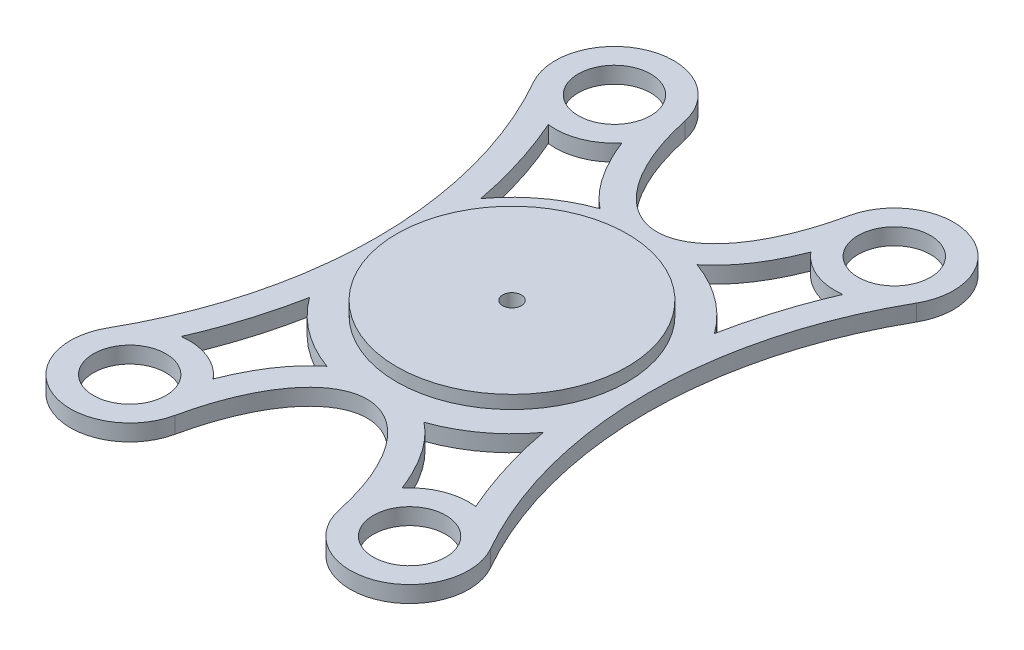
SolidWorks part; units mm, degrees
material "ABS"
ref_plane "Front Plane" through (0, 0, 0) normal (0, 0, 1) x (1, 0, 0)
ref_plane "Top Plane" through (0, 0, 0) normal (0, 1, 0) x (1, 0, 0)
ref_plane "Right Plane" through (0, 0, 0) normal (1, 0, 0) x (0, 0, -1)
sketch "Sketch1" plane through (0, 0, 0) normal (0, 1, 0) x (1, 0, 0)
  line L1 (-50, -50) -> (50, -50)
  line L2 (-50, -50) -> (-50, 50)
  line L3 (-50, 50) -> (50, 50)
  line L4 (50, -50) -> (50, 50)
  line L5 (-50, -50) -> (50, 50) construction
  line L6 (-50, 50) -> (50, -50) construction
  point P0 (0, 0)
  dimension "D1" = 100
  dimension "D2" = 100
extrude "Boss-Extrude1" add sketch "Sketch1" along normal blind 2.5
sketch "Sketch2" plane through (0, 2.5, 0) normal (0, 1, 0) x (1, 0, 0)
  line L0 (50, 50) -> (-50, 50) construction
  line L1 (-50, -50) -> (50, -50) construction
  line L2 (-21.25, 36.8061) -> (21.25, -36.8061)
  line L3 (21.25, 36.8061) -> (-21.25, -36.8061)
  line L14 (0, -15.9125) -> (0, 15.9125)
  arc A0 (-29.0749, 32.3597) -> (-12.4502, 38.6938) centre (-21.25, 36.8061) cw
  circle A1 centre (21.25, 36.8061) radius 5.5
  circle A2 centre (-21.25, 36.8061) radius 5.5
  circle A3 centre (21.25, -36.8061) radius 5.5
  circle A4 centre (-21.25, -36.8061) radius 5.5
  arc A5 (12.4502, 38.6938) -> (29.0749, 32.3597) centre (21.25, 36.8061) cw
  arc A6 (-12.4502, -38.6938) -> (-29.0749, -32.3597) centre (-21.25, -36.8061) cw
  arc A7 (12.4502, -38.6938) -> (29.0749, -32.3597) centre (21.25, -36.8061) ccw
  arc A8 (29.0749, 32.3597) -> (29.0749, -32.3597) centre (86.0232, 0) ccw
  arc A9 (-29.0749, 32.3597) -> (-29.0749, -32.3597) centre (-86.0232, 0) cw
  ellipse E0 centre (0, 50) end of major axis (0, 22) minor radius 13.609 (-12.4502, 38.6938) -> (12.4502, 38.6938) ccw
  ellipse E1 centre (0, -50) end of major axis (0, -22) minor radius 13.609 (12.4502, -38.6938) -> (-12.4502, -38.6938) ccw
  point P11 (0, 0)
  point P12 (0, 0)
  point P33 (0, 0)
  point P41 (0, 0)
  dimension "D4" = 11
  dimension "D1" = 9
  dimension "D7" = 65.5
  dimension "D8" = 65.5
  dimension "D2" = 28
  dimension "D3" = 85
  dimension "D5" = 31.8249
  dimension "D6" = 60
  dimension "D9" = 28
extrude "Cut-Extrude1" cut sketch "Sketch2" against normal blind 10
sketch "Sketch4" plane through (0, 2.5, 0) normal (0, 1, 0) x (1, 0, 0)
  arc A0 (-29.0749, -32.3597) -> (-12.4502, -38.6938) centre (-21.25, -36.8061) ccw construction
  arc A1 (-17.7495, -12.9983) -> (-7.3676, -20.7296) centre (0, 0) ccw
  arc A2 (7.3676, -20.7296) -> (17.7495, -12.9983) centre (0, 0) ccw
  arc A3 (-22.3579, -27.8745) -> (-14.3451, -31.0336) centre (-21.25, -36.8061) cw
  arc A4 (22.3579, -27.8745) -> (14.3451, -31.0336) centre (21.25, -36.8061) ccw
  arc A5 (14.3451, 31.0336) -> (22.3579, 27.8745) centre (21.25, 36.8061) ccw
  arc A6 (-14.3451, 31.0336) -> (-22.3579, 27.8745) centre (-21.25, 36.8061) cw
  arc A7 (17.7495, 12.9983) -> (7.3676, 20.7296) centre (0, 0) ccw
  arc A8 (-7.3676, 20.7296) -> (-17.7495, 12.9983) centre (0, 0) ccw
  spline S0 degree 3 poles (7.3676, 20.7296) (7.7472, 21.0301) (8.1145, 21.3503) (9.2471, 22.428) (9.9675, 23.253) (11.9755, 25.9455) (13.1132, 28.0315) (14.1613, 30.5689) (14.2541, 30.8002) (14.3451, 31.0336) knots 0.658937 0.658937 0.658937 0.658937 0.6875 0.6875 0.75 0.75 0.875 0.875 0.887406 0.887406 0.887406 0.887406
  spline S1 degree 3 poles (-17.7495, -12.9983) (-18.73, -18.1485) (-20.279, -23.1263) (-22.3579, -27.8745) knots 0.6785 0.6785 0.6785 0.6785 0.896036 0.896036 0.896036 0.896036 weights 0.943039 0.949799 0.960677 0.975675
  spline S2 degree 3 poles (17.7495, 12.9983) (18.73, 18.1485) (20.279, 23.1263) (22.3579, 27.8745) knots 0.6785 0.6785 0.6785 0.6785 0.896036 0.896036 0.896036 0.896036 weights 0.943039 0.949799 0.960677 0.975675
  spline S3 degree 3 poles (-1432.768, 4724.087) (-243.33, -633.9868) (54.7255, -128.7666) (13.1132, -28.0315) (11.9755, -25.9455) (9.9675, -23.253) (9.2471, -22.428) (7.6924, -20.9487) (6.8575, -20.294) (5.0662, -19.1991) (4.1085, -18.7595) (2.1008, -18.1589) (1.0511, -18) (-1.0511, -18) (-2.1008, -18.1589) (-4.1085, -18.7595) (-5.0662, -19.1991) (-6.8575, -20.294) (-7.6924, -20.9487) (-9.2471, -22.428) (-9.9675, -23.253) (-11.9755, -25.9455) (-13.1132, -28.0315) (-54.7252, -128.766) (243.3266, -633.9809) (1432.7472, 4723.9934) knots -5.205158 -5.205158 -5.205158 -5.205158 0.125 0.125 0.25 0.25 0.3125 0.3125 0.375 0.375 0.4375 0.4375 0.5 0.5 0.5625 0.5625 0.625 0.625 0.6875 0.6875 0.75 0.75 0.875 0.875 6.205127 6.205127 6.205127 6.205127 only from (16.3612, -37.8548) to (-16.3612, -37.8548)
  spline S4 degree 3 poles (14.3451, -31.0336) (14.2541, -30.8002) (14.1613, -30.5689) (13.1132, -28.0315) (11.9755, -25.9455) (9.9675, -23.253) (9.2471, -22.428) (8.1145, -21.3503) (7.7472, -21.0301) (7.3676, -20.7296) knots 0.112594 0.112594 0.112594 0.112594 0.125 0.125 0.25 0.25 0.3125 0.3125 0.341063 0.341063 0.341063 0.341063
  spline S5 degree 3 poles (-7.3676, -20.7296) (-7.7472, -21.0301) (-8.1145, -21.3503) (-9.2471, -22.428) (-9.9675, -23.253) (-11.9755, -25.9455) (-13.1132, -28.0315) (-14.1613, -30.5689) (-14.2541, -30.8002) (-14.3451, -31.0336) knots 0.658937 0.658937 0.658937 0.658937 0.6875 0.6875 0.75 0.75 0.875 0.875 0.887406 0.887406 0.887406 0.887406
  spline S19 degree 3 poles (-25.5972, 34.3359) (-13.2101, 12.5365) (-13.2101, -12.5365) (-25.5972, -34.3359) knots 0 0 0 0 1 1 1 1 weights 1 0.912959 0.912959 1
  spline S20 degree 3 poles (-22.3579, 27.8745) (-20.279, 23.1263) (-18.73, 18.1485) (-17.7495, 12.9983) knots 0.103964 0.103964 0.103964 0.103964 0.3215 0.3215 0.3215 0.3215 weights 0.975675 0.960677 0.949799 0.943039
  spline S25 degree 3 poles (25.5972, -34.3359) (13.2101, -12.5365) (13.2101, 12.5365) (25.5972, 34.3359) knots 0 0 0 0 1 1 1 1 weights 1 0.912959 0.912959 1
  spline S26 degree 3 poles (22.3579, -27.8745) (20.279, -23.1263) (18.73, -18.1485) (17.7495, -12.9983) knots 0.103964 0.103964 0.103964 0.103964 0.3215 0.3215 0.3215 0.3215 weights 0.975675 0.960677 0.949799 0.943039
  spline S28 degree 3 poles (1432.768, -4724.087) (243.33, 633.9868) (-54.7255, 128.7666) (-13.1132, 28.0315) (-11.9755, 25.9455) (-9.9675, 23.253) (-9.2471, 22.428) (-7.6924, 20.9487) (-6.8575, 20.294) (-5.0662, 19.1991) (-4.1085, 18.7595) (-2.1008, 18.1589) (-1.0511, 18) (1.0511, 18) (2.1008, 18.1589) (4.1085, 18.7595) (5.0662, 19.1991) (6.8575, 20.294) (7.6924, 20.9487) (9.2471, 22.428) (9.9675, 23.253) (11.9755, 25.9455) (13.1132, 28.0315) (54.7252, 128.766) (-243.3266, 633.9809) (-1432.7472, -4723.9934) knots -5.205158 -5.205158 -5.205158 -5.205158 0.125 0.125 0.25 0.25 0.3125 0.3125 0.375 0.375 0.4375 0.4375 0.5 0.5 0.5625 0.5625 0.625 0.625 0.6875 0.6875 0.75 0.75 0.875 0.875 6.205127 6.205127 6.205127 6.205127 only from (-16.3612, 37.8548) to (16.3612, 37.8548)
  spline S29 degree 3 poles (-14.3451, 31.0336) (-14.2541, 30.8002) (-14.1613, 30.5689) (-13.1132, 28.0315) (-11.9755, 25.9455) (-9.9675, 23.253) (-9.2471, 22.428) (-8.1145, 21.3503) (-7.7472, 21.0301) (-7.3676, 20.7296) knots 0.112594 0.112594 0.112594 0.112594 0.125 0.125 0.25 0.25 0.3125 0.3125 0.341063 0.341063 0.341063 0.341063
  dimension "D5" = 44
  dimension "D1" = 4
  dimension "D2" = 4
  dimension "D3" = 4
  dimension "D4" = 4
extrude "Cut-Extrude3" cut sketch "Sketch4" against normal blind 10
sketch "Sketch6" plane through (0, 2.5, 0) normal (0, 1, 0) x (1, 0, 0)
  circle A0 centre (0, 0) radius 17.5
  dimension "D1" = 35
extrude "Boss-Extrude11" add sketch "Sketch6" along normal blind 2 and the other way blind 5
sketch "Sketch7" plane through (0, 4.5, 0) normal (0, 1, 0) x (1, 0, 0)
  circle A0 centre (0, 0) radius 1.425
  dimension "D1" = 2.85
extrude "Cut-Extrude4" cut sketch "Sketch7" against normal through all
